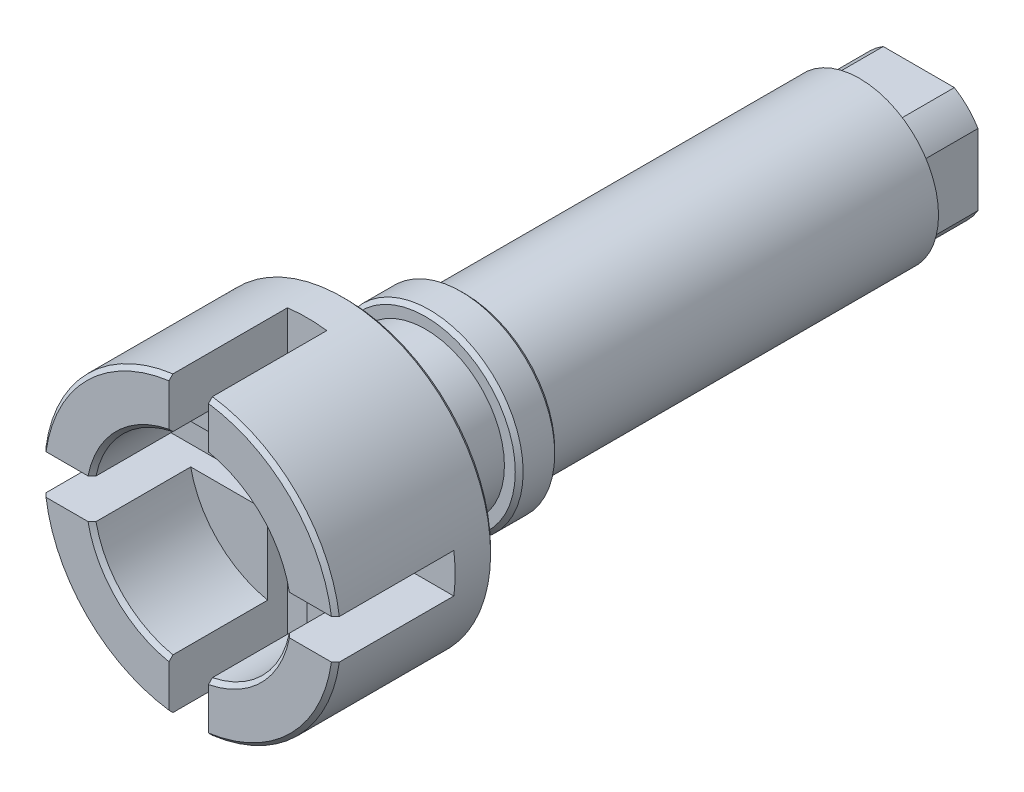
SolidWorks part; units mm, degrees
material "SUS304"
ref_plane "Front Plane" through (0, 0, 0) normal (0, 0, 1) x (1, 0, 0)
ref_plane "Top Plane" through (0, 0, 0) normal (0, 1, 0) x (1, 0, 0)
ref_plane "Right Plane" through (0, 0, 0) normal (1, 0, 0) x (0, 0, -1)
sketch "Sketch1" plane through (0, 0, 0) normal (0, 0, 1) x (1, 0, 0)
  circle A0 centre (0, 0) radius 7.5
  dimension "D1" = 15
extrude "Boss-Extrude1" add sketch "Sketch1" against normal blind 37
sketch "Sketch2" plane through (0, 0, 0) normal (0, 1, 0) x (1, 0, 0)
  line L0 (7.5, 37) -> (-7.5, 37) construction
  line L1 (7.5, 37) -> (4, 37)
  line L2 (7.5, 37) -> (7.5, 8)
  line L3 (7.5, 8) -> (4, 8)
  line L4 (4, 37) -> (4, 8)
  line L5 (0, 0) -> (0, 55.0925) construction
  line L6 (-7.5, 0) -> (7.5, 0) construction
  dimension "D1" = 8
  dimension "D2" = 4
revolve "Cut-Revolve1" cut sketch "Sketch2" angle 360 about L5
sketch "Sketch4" plane through (0, 0, 0) normal (0, 0, 1) x (1, 0, 0)
  line L0 (-9.6465, 0) -> (9.6465, 0) construction
  line L1 (-9.6465, 1) -> (9.6465, 1)
  line L2 (-9.6465, -1) -> (9.6465, -1)
  arc A0 (-9.6465, 1) -> (-9.6465, -1) centre (-9.6465, 0) ccw
  arc A1 (9.6465, -1) -> (9.6465, 1) centre (9.6465, 0) ccw
  point P2 (0, 0)
  dimension "D1" = 2
extrude "Cut-Extrude1" cut sketch "Sketch4" against normal blind 6
sketch "Sketch5" plane through (0, 0, 0) normal (0, 0, 1) x (1, 0, 0)
  line L0 (0, 8.5) -> (0, -8.5) construction
  line L1 (1, 8.5) -> (1, -8.5)
  line L2 (-1, 8.5) -> (-1, -8.5)
  arc A0 (1, 8.5) -> (-1, 8.5) centre (0, 8.5) ccw
  arc A1 (-1, -8.5) -> (1, -8.5) centre (0, -8.5) ccw
  point P2 (0, 0)
  dimension "D1" = 17
  dimension "D2" = 2
extrude "Cut-Extrude2" cut sketch "Sketch5" against normal blind 6
sketch "Sketch6" plane through (0, 0, 0) normal (0, 0, 1) x (1, 0, 0)
  circle A0 centre (0, 0) radius 5
  dimension "D1" = 10
extrude "Cut-Extrude3" cut sketch "Sketch6" against normal blind 5
sketch "Sketch10" plane through (0, 0, -37) normal (0, 0, -1) x (-1, 0, 0)
  line L1 (-3, 3) -> (3, 3)
  line L2 (-3, 3) -> (-3, -3)
  line L3 (-3, -3) -> (3, -3)
  line L4 (3, 3) -> (3, -3)
  line L5 (-3, 3) -> (3, -3) construction
  line L6 (-3, -3) -> (3, 3) construction
  point P0 (0, 0)
  dimension "D1" = 6
  dimension "D2" = 6
extrude "Cut-Extrude4" cut sketch "Sketch10" against normal blind 3 flip side to cut
sketch "Sketch19" plane through (0, 0, -34) normal (0, 0, -1) x (-1, 0, 0)
  circle A0 centre (0, 0) radius 4.9099
  circle A1 centre (0, 0) radius 3.5
  dimension "D1" = 7
extrude "Cut-Extrude5" cut sketch "Sketch19" along normal through all
hole_wizard "M4x0.7 Tapped Hole1" positions "Sketch7" profile "Sketch9" tap size "M4x0.7" standard "ANSI Metric"
sketch "Sketch7" plane through (0, 0, -37) normal (0, 0, -1) x (-1, 0, 0)
  point P0 (0, 0)
sketch "Sketch9" plane through (0, 0, -37) normal (1, 0, 0) x (0, 1, 0)
  line L0 (0, 0) -> (0, 11.0914)
  line L1 (0, 11.0914) -> (1.65, 10.1)
  line L2 (1.65, 10.1) -> (1.65, 0)
  line L5 (1.65, 0) -> (0, 0)
  line L10 (0, 11.0914) -> (-1.65, 10.1) construction
  line L11 (0, -6.35) -> (0, 107.95) construction
  dimension "Tap Drill Dia." = 3.3
  dimension "Tap Drill Depth" = 10.1
  dimension "Drill Angle" = 118
cosmetic thread "Hole Thread1" parameters "D1"=8, "D2"=4
sketch "Sketch17" plane through (0, 0, 0) normal (0, 1, 0) x (1, 0, 0)
  line L0 (4, 8) -> (4, 34) construction
  line L1 (4, 14) -> (4.75, 14)
  line L2 (4, 14) -> (4, 12)
  line L3 (4, 12) -> (4.75, 12)
  line L4 (4.75, 14) -> (4.75, 12)
  line L5 (1.8028, 37) -> (-1.8028, 37) construction
  line L6 (0, 0) -> (0, 58.8551) construction
  dimension "D1" = 4.75
  dimension "D2" = 2
  dimension "D3" = 23
revolve "Revolve1" add sketch "Sketch17" angle 360 about L6
chamfer "Chamfer1" distance 0.2 angle 45 2 edges at (4.75, 0, -12) (4.75, 0, -14)
chamfer "Chamfer2" distance 0.2 angle 45 9 edges at (3.5355, -3.5355, 0) (3.5355, 3.5355, 0) (-3.5355, 3.5355, 0) (-3.5355, -3.5355, 0) (5.3033, -5.3033, 0) (-5.3033, -5.3033, 0) (-5.3033, 5.3033, 0) (5.3033, 5.3033, 0) (7.5, 0, -8)
